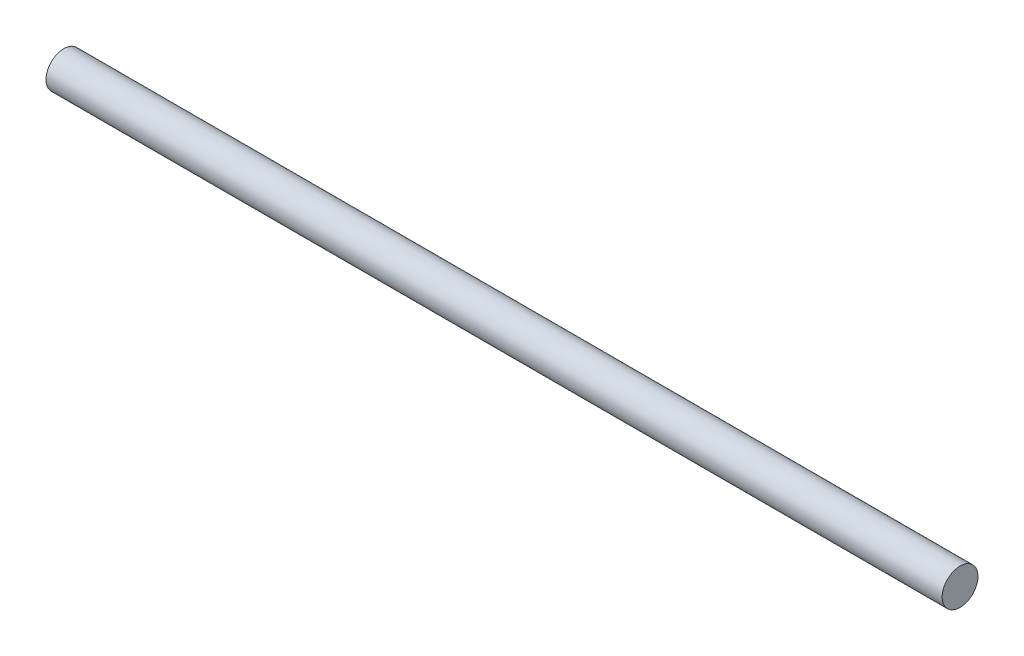
SolidWorks part; units mm, degrees
ref_plane "Front Plane" through (0, 0, 0) normal (0, 0, 1) x (1, 0, 0)
ref_plane "Top Plane" through (0, 0, 0) normal (0, 1, 0) x (1, 0, 0)
ref_plane "Right Plane" through (0, 0, 0) normal (1, 0, 0) x (0, 0, -1)
sketch "Sketch1" plane through (0, 0, 0) normal (1, 0, 0) x (0, 0, -1)
  circle A0 centre (0, 0) radius 5
  dimension "D1" = 10
extrude "Boss-Extrude1" add sketch "Sketch1" along normal blind 250
